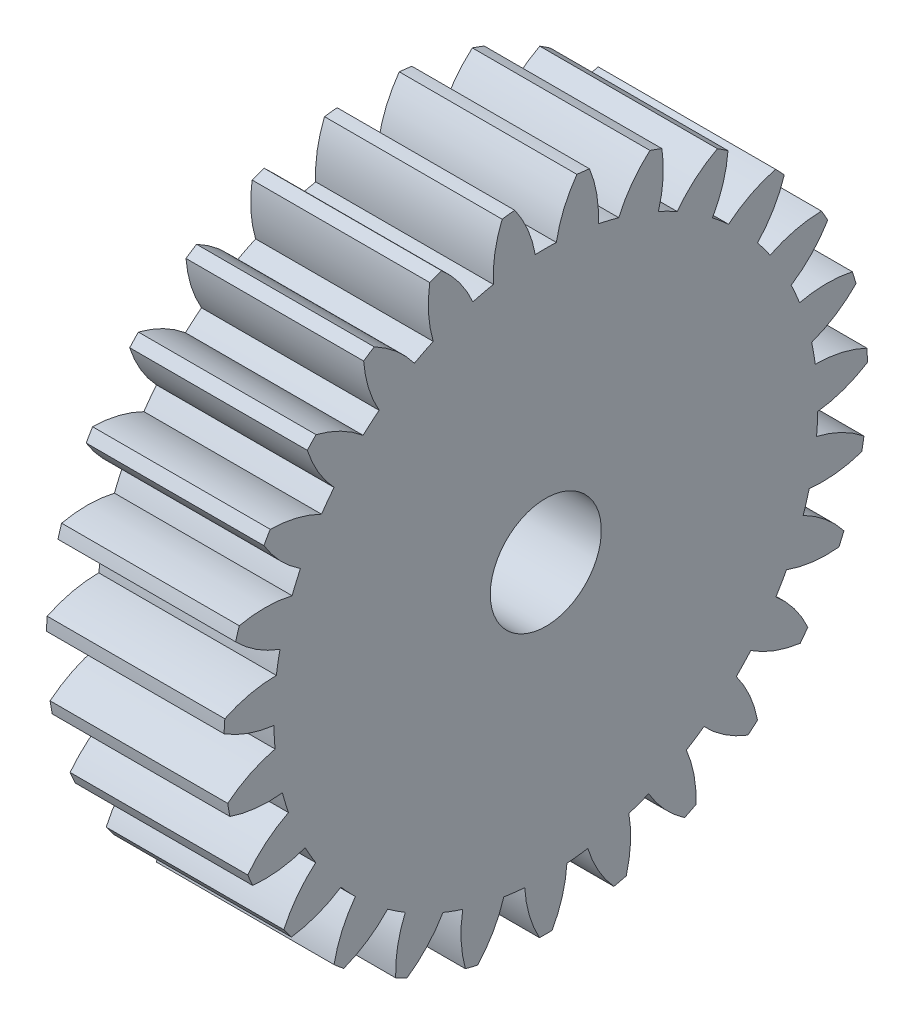
SolidWorks part; units mm, degrees
ref_plane "Plane1" through (0, 0, 0) normal (0, 0, 1) x (1, 0, 0)
ref_plane "Plane2" through (0, 0, 0) normal (0, 1, 0) x (1, 0, 0)
ref_plane "Plane3" through (0, 0, 0) normal (1, 0, 0) x (0, 0, -1)
other "Configuration Table"
sketch "HoldingSke" plane through (0, 0, 0) normal (0, 1, 0) x (1, 0, 0)
  line L0 (0, 0) -> (0.891, -0.454)
  line L1 (-15, 0) -> (100, 0) construction
  line L2 (0, 0) -> (-2.1039, 2.3779)
  line L3 (0, 0) -> (-11.863, 4.5341)
  line L4 (0, 0) -> (7.6947, 3.9207)
  line L5 (0, 0) -> (-46.8476, -17.4728)
  line L6 (0, 0) -> (-6.6317, -4.4744)
  line L7 (-2.1039, 2.3779) -> (8.6586, 51.2059)
  line L8 (-76.2, 54.61) -> (-75.3, 54.61)
  line L9 (-71.009, 38.7566) -> (-53.1078, 45.2721)
  line L10 (-76.2, 71.12) -> (104.1128, 71.12)
  line L11 (0, 0) -> (-8, 0)
  line L12 (-76.2, 101.6) -> (-76.162, 101.6)
  line L13 (24.9733, 27.94) -> (52.9518, 28.4284)
  line L14 (24.9733, 27.94) -> (24.9743, 27.94)
  line L15 (24.9733, 27.94) -> (100.4006, 29.5858)
  line L16 (-63.627, -1) -> (-12.827, -1)
  circle A0 centre (0, 0) radius 2.5
  circle A1 centre (0, 0) radius 12.249
  circle A2 centre (0, 0) radius 37.5
  circle A3 centre (0, 0) radius 2.5
  dimension "MHD" = 24.498
  dimension "Hub_dia" = 75
  dimension "Bore" = 5
  dimension "MBD" = 5
  dimension "Num_teeth" = 27
  dimension "Pitch" = 1
  dimension "Overall_len" = 50
  dimension "Show_teeth" = 27
  dimension "Thickness" = 8
  dimension "OAL" = 50.0001
  dimension "T_dim" = 0.9
  dimension "Ap" = 20
  dimension "H" = 19.05
  dimension "Pitch_radius" = 180.3128
  dimension "Width" = 8
  dimension "Backlash" = 0.038
  dimension "Addendum_fac" = 1
  dimension "Dedendum_fac" = 1.25
  dimension "Clearance_fac" = 0.25
  dimension "Dedendum_add" = 0.001
  dimension "Module" = 1
sketch "BasProSke" plane through (0, 0, 0) normal (0, 1, 0) x (1, 0, 0)
  line L0 (-10, 0) -> (60, 0) construction
  line L1 (0, 0) -> (0, 14.5)
  line L2 (0, 0) -> (8, 0)
  line L3 (8, 0) -> (8, 14.5)
  line L4 (8, 14.5) -> (0, 14.5)
  dimension "Thickness" = 8
  dimension "Diameter" = 29
revolve "Base-Revolve" add sketch "BasProSke" angle 360 about L0
sketch "TooCutSke" plane through (0, 0, 0) normal (1, 0, 0) x (0, 0, -1)
  line L1 (0, 0) -> (0, 107) construction
  line L2 (0, 0) -> (-0.8514, 13.4731) construction
  line L3 (0, 0) -> (-3.1301, 26.7794) construction
  line L4 (-0.8514, 13.4731) -> (-1.565, 13.3897) construction
  arc A0 (0.4741, 12.2398) -> (-0.4741, 12.2398) centre (0, 0) ccw
  arc A1 (1.4167, 14.4561) -> (-1.4167, 14.4561) centre (0, 0) ccw
  circle A2 centre (0, 0) radius 13.5 construction
  circle A3 centre (0, 0) radius 12.6859 construction
  arc A4 (-0.4741, 12.2398) -> (-1.4167, 14.4561) centre (-5.7895, 11.2877) ccw
  arc A5 (1.4167, 14.4561) -> (0.4741, 12.2398) centre (5.7895, 11.2877) ccw
  dimension "Root_dia" = 24.498
  dimension "Overcut_dia" = 29.0508
  dimension "Pitch_dia" = 27
  dimension "Base_dia" = 25.3717
  dimension "Flank_rad" = 5.4
  dimension "Half_ang" = 6.667
  dimension "Half_CT" = 0.7185
extrude "ToothCut" cut sketch "TooCutSke" along normal through all
fillet "Breaks" [suppressed] radius 0.02
fillet "RootFillets" [suppressed] radius 0.251
pattern_circular "TeethCuts" count 27 every 13.333 about axis through (-10, 0, 0) along (1, 0, 0) of "ToothCut", "RootFillets", "Breaks"
sketch "HubNeaOneSke" plane through (0, 0, 0) normal (-1, 0, 0) x (0, 0, 1)
  circle A0 centre (0, 0) radius 12.249
  dimension "Diameter" = 24.498
extrude "HubNearOne" [suppressed] add sketch "HubNeaOneSke" along normal blind 42.0001
sketch "HubNeaBotSke" plane through (0, 0, 0) normal (-1, 0, 0) x (0, 0, 1)
  circle A0 centre (0, 0) radius 12.249
  dimension "Diameter" = 24.498
extrude "HubNearBoth" [suppressed] add sketch "HubNeaBotSke" along normal blind 21
ref_plane "FarPln" through (8, 0, 0) normal (1, 0, 0) x (0, 0, -1)
sketch "HubFarSke" plane through (8, 0, 0) normal (1, 0, 0) x (0, 0, -1)
  circle A0 centre (0, 0) radius 12.249
  dimension "Diameter" = 24.498
extrude "HubFar" [suppressed] add sketch "HubFarSke" along normal blind 21
sketch "BorSke" plane through (0, 0, 0) normal (1, 0, 0) x (0, 0, -1)
  circle A0 centre (0, 0) radius 2.5
  dimension "Diameter" = 5
extrude "Bore" cut sketch "BorSke" along normal mid plane 100.0001
sketch "KeySke" plane through (0, 0, 0) normal (1, 0, 0) x (0, 0, -1)
  line L0 (-1, 0) -> (-1, 3.4)
  line L1 (-1, 3.4) -> (1, 3.4)
  line L2 (1, 3.4) -> (1, 0)
  line L3 (0, 0) -> (0, 34) construction
  line L4 (-1, 0) -> (1, 0)
  dimension "Offset" = 3.4
  dimension "Width" = 2
extrude "Keyway" [suppressed] cut sketch "KeySke" along normal mid plane 100.0001
pattern_circular "Keyway2" [suppressed] count 2 every 90 about axis through (-10, 0, 0) along (1, 0, 0)
equation "' \"Module@HoldingSke\" = 6.35"
equation "' \"Num_teeth@HoldingSke\" = 12"
equation "' \"Ap@HoldingSke\" =  20"
equation "' \"Ap@HoldingSke\" = 20"
equation "' \"Width@HoldingSke\" = 0.5 * 25.4"
equation "' \"Hub_dia@HoldingSke\"= 1 * 25.4"
equation "' \"Hub_dia@HoldingSke\" = 1 * 25.4"
equation "' \"Overall_len@HoldingSke\" = 1.0 * 25.4"
equation "' \"Bore@HoldingSke\" = 0.75 * 25.4"
equation "' \"T_dim@HoldingSke\" = 0.1 * 25.4"
equation "' \"Width@KeySke\" = 0.25 * 25.4"
equation "' \"Show_teeth@HoldingSke\" = 13"
equation "' \"Backlash@HoldingSke\" = 0.009 * 25.4"
equation "' \"Addendum_fac@HoldingSke\" = 1.0"
equation "' \"Dedendum_fac@HoldingSke\" = 1.25"
equation "' \"Dedendum_add@HoldingSke\" = 0.00005 * 25.4"
equation "' \"Clearance_fac@HoldingSke\" = 0.25"
equation "\"Pitch@HoldingSke\" = 1 / \"Module@HoldingSke\""
equation "\"Overcut_dia@TooCutSke\" = (\"Num_teeth@HoldingSke\" + 2 * \"Addendum_fac@HoldingSke\") / \"Pitch@HoldingSke\" + 0.002 * 25.4"
equation "\"Pitch_dia@TooCutSke\" = \"Num_teeth@HoldingSke\" / \"Pitch@HoldingSke\""
equation "\"Base_dia@TooCutSke\" = \"Num_teeth@HoldingSke\" / \"Pitch@HoldingSke\" * cos((\"Ap@HoldingSke\"  * 3.14159265 / 180))"
equation "\"Root_dia@TooCutSke\" = (\"Num_teeth@HoldingSke\" + 2) / \"Pitch@HoldingSke\" - 2 * (\"Addendum_fac@HoldingSke\" + \"Dedendum_fac@HoldingSke\") / \"Pitch@HoldingSke\" - \"Dedendum_add@HoldingSke\" * 2"
equation "\"Half_ang@TooCutSke\" = 180 / \"Num_teeth@HoldingSke\""
equation "\"Half_CT@TooCutSke\" = \"Num_teeth@HoldingSke\" / \"Pitch@HoldingSke\" * sin((3.14159265 / 2 / \"Num_teeth@HoldingSke\")) / 2 - 7 * \"Backlash@HoldingSke\" / 4"
equation "\"Flank_rad@TooCutSke\" = \"Num_teeth@HoldingSke\" / \"Pitch@HoldingSke\" / 5"
equation "\"Radius@RootFillets\" = \"Clearance_fac@HoldingSke\" / \"Pitch@HoldingSke\" + \"Dedendum_add@HoldingSke\""
equation "\"Break_rad@Breaks\" = 0.02 / \"Pitch@HoldingSke\""
equation "\"Thickness@HoldingSke\" = \"Width@HoldingSke\""
equation "\"OAL@HoldingSke\" = \"Thickness@HoldingSke\""
equation "\"MHD@HoldingSke\" = (\"Num_teeth@HoldingSke\" + 2) / \"Pitch@HoldingSke\" - 2 * (\"Addendum_fac@HoldingSke\" + \"Dedendum_fac@HoldingSke\")  / \"Pitch@HoldingSke\" - \"Dedendum_add@HoldingSke\" * 2"
equation "\"MBD@HoldingSke\" = (\"Num_teeth@HoldingSke\" + 2) / \"Pitch@HoldingSke\" - 2 * (\"Addendum_fac@HoldingSke\" + \"Dedendum_fac@HoldingSke\")  / \"Pitch@HoldingSke\" - \"Dedendum_add@HoldingSke\" * 2 - 0.002 * 25.4"
equation "\"MHD@HoldingSke\" = ((sgn( \"MHD@HoldingSke\" - \"Hub_dia@HoldingSke\" )-1)*( \"MHD@HoldingSke\" - \"Hub_dia@HoldingSke\" ))/-2+ \"Hub_dia@HoldingSke\""
equation "\"MBD@HoldingSke\" = ((sgn( \"MBD@HoldingSke\" - \"Bore@HoldingSke\" )-1)*( \"MBD@HoldingSke\" - \"Bore@HoldingSke\" ))/-2+ \"Bore@HoldingSke\""
equation "\"OAL@HoldingSke\" = ((sgn( \"OAL@HoldingSke\" - \"Overall_len@HoldingSke\" )+1)*( \"OAL@HoldingSke\" - \"Overall_len@HoldingSke\" ))/2 + \"Overall_len@HoldingSke\" + 0.000002 * 25.4"
equation "\"Num_teeth@TeethCuts\" = int( \"Show_teeth@HoldingSke\" ) + 1"
equation "\"Num_teeth@TeethCuts\" = ((sgn( \"Num_teeth@TeethCuts\" - \"Num_teeth@HoldingSke\" )-1)*( \"Num_teeth@TeethCuts\" - \"Num_teeth@HoldingSke\" ))/-2+ \"Num_teeth@HoldingSke\""
equation "\"Num_teeth@TeethCuts\" = ((sgn( \"Num_teeth@TeethCuts\" - 2.0)+1)*( \"Num_teeth@TeethCuts\" - 2.0))/2 +2.0"
equation "\"Angle@TeethCuts\" = 360.0 / \"Num_teeth@HoldingSke\""
equation "\"Diameter@BasProSke\" = (\"Num_teeth@HoldingSke\" + 2 * \"Addendum_fac@HoldingSke\") / \"Pitch@HoldingSke\""
equation "\"Thickness@BasProSke\"  = \"Thickness@HoldingSke\""
equation "' \"Fillet_rad@BasProSke\" =  \"Thickness@HoldingSke\" * 0.05"
equation "' \"Fillet_rad@BasProSke\" = \"Thickness@HoldingSke\" * 0.05"
equation "\"MHD@HoldingSke\" = ((sgn( \"MHD@HoldingSke\" - \"Root_dia@TooCutSke\" )-1)*( \"MHD@HoldingSke\" - \"Root_dia@TooCutSke\" ))/-2+ \"Root_dia@TooCutSke\""
equation "\"Diameter@HubNeaOneSke\" = \"MHD@HoldingSke\""
equation "\"Length@HubNearOne\" = \"OAL@HoldingSke\" - \"Thickness@BasProSke\""
equation "\"Diameter@HubNeaBotSke\" = \"MHD@HoldingSke\""
equation "\"Length@HubNearBoth\" = ( \"OAL@HoldingSke\" - \"Thickness@BasProSke\" ) / 2.0"
equation "\"Thickness@FarPln\" = \"Thickness@BasProSke\""
equation "\"Diameter@HubFarSke\" = \"MHD@HoldingSke\""
equation "\"Length@HubFar\" = ( \"OAL@HoldingSke\" - \"Thickness@BasProSke\" ) / 2.0"
equation "\"Diameter@BorSke\" = \"MBD@HoldingSke\""
equation "\"D1@Bore\" = \"OAL@HoldingSke\" * 2.0"
equation "\"D1@Keyway\" = \"OAL@HoldingSke\" * 2.0"
equation "\"Offset@KeySke\" = \"T_dim@HoldingSke\" + \"MBD@HoldingSke\" / 2.0"
